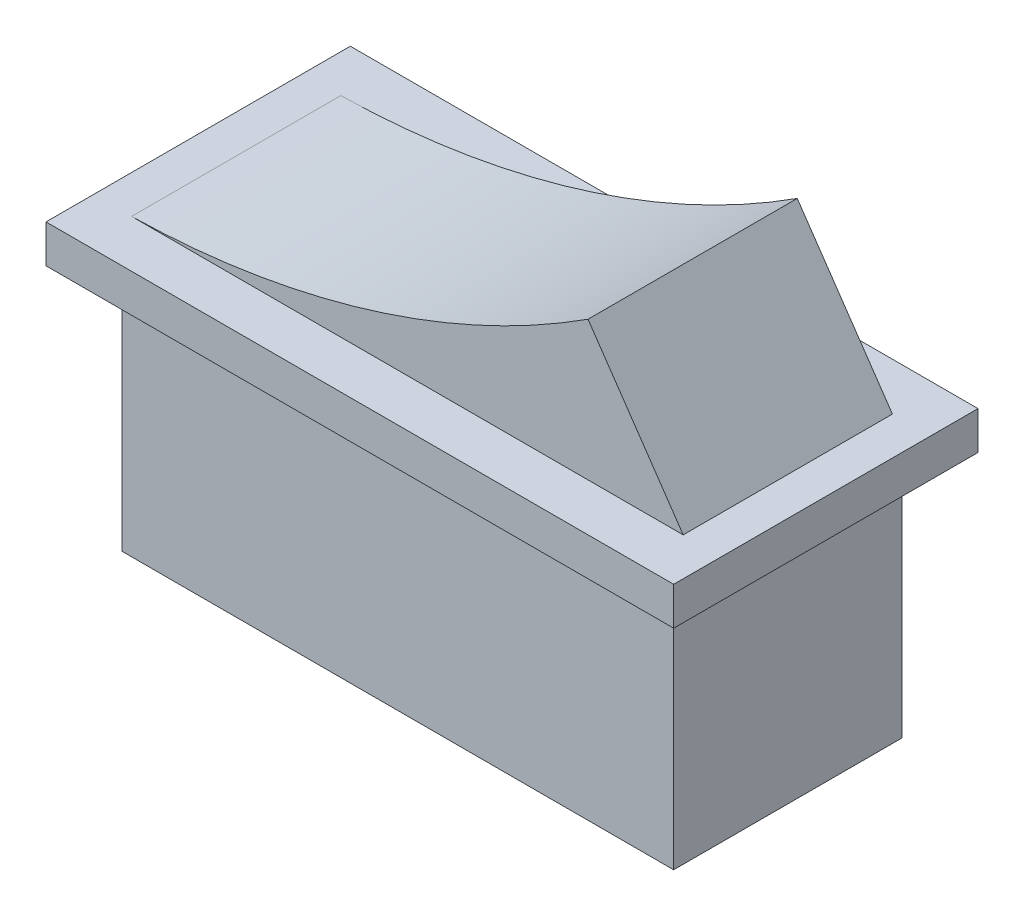
SolidWorks part; units mm, degrees
ref_plane "前视基准面" through (0, 0, 0) normal (0, 0, 1) x (1, 0, 0)
ref_plane "上视基准面" through (0, 0, 0) normal (0, 1, 0) x (1, 0, 0)
ref_plane "右视基准面" through (0, 0, 0) normal (1, 0, 0) x (0, 0, -1)
sketch "草图1" plane through (0, 0, 0) normal (0, 1, 0) x (1, 0, 0)
  line L1 (-16.5, 8) -> (16.5, 8)
  line L2 (-16.5, 8) -> (-16.5, -8)
  line L3 (-16.5, -8) -> (16.5, -8)
  line L4 (16.5, 8) -> (16.5, -8)
  point P4 (0, 8)
  point P6 (-16.5, 0)
  dimension "D1" = 16
  dimension "D2" = 33
extrude "凸台-拉伸1" add sketch "草图1" along normal blind 2
sketch "草图2" plane through (0, 0, 0) normal (0, 0, 1) x (1, 0, 0)
  line L0 (-14.5, 2) -> (14.5, 2)
  line L1 (-16.5, 2) -> (16.5, 2) construction
  line L2 (14.5, 2) -> (9.4969, 9.3175)
  arc A0 (-14.5, 2) -> (9.4969, 9.3175) centre (-15.4049, 47.9739) ccw
  point P4 (0, 2)
  dimension "D1" = 29
extrude "凸台-拉伸2" add sketch "草图2" along normal mid plane 11 contours A0 L0 L2
sketch "草图3" plane through (0, 0, 0) normal (0, 1, 0) x (1, 0, 0)
  line L1 (-14.5, -6) -> (14.5, -6)
  line L2 (-14.5, -6) -> (-14.5, 6)
  line L3 (-14.5, 6) -> (14.5, 6)
  line L4 (14.5, -6) -> (14.5, 6)
  point P4 (0, -6)
  point P6 (-14.5, 0)
  dimension "D1" = 12
  dimension "D2" = 29
extrude "凸台-拉伸3" add sketch "草图3" against normal blind 13
